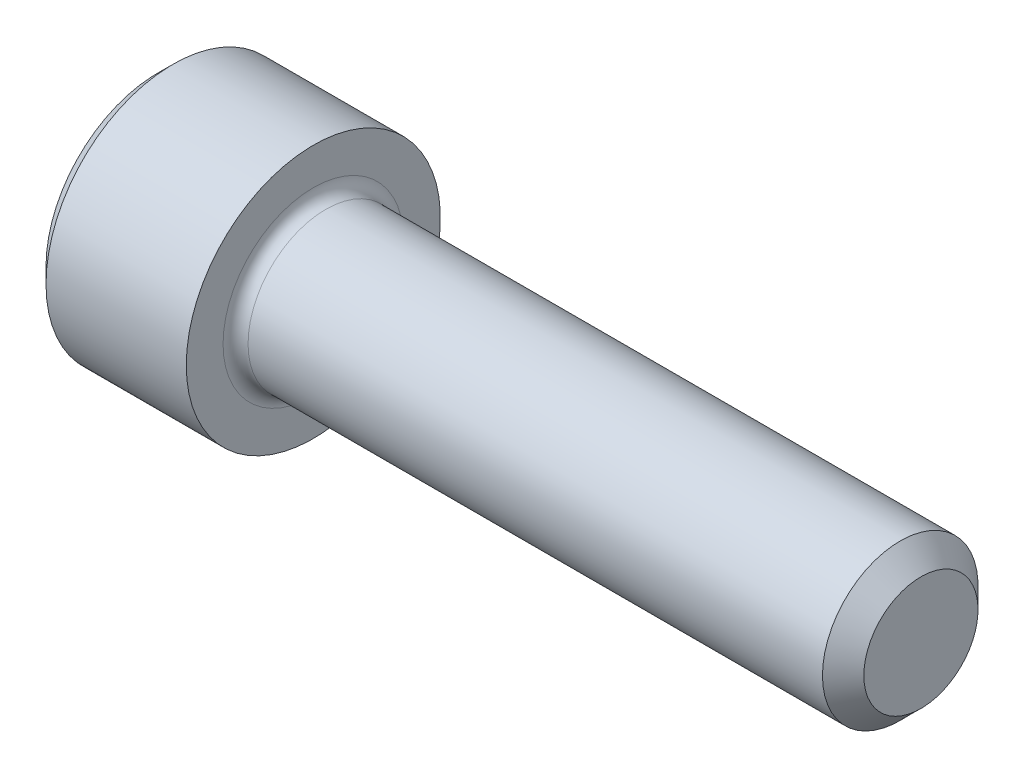
SolidWorks part; units mm, degrees
ref_plane "Plane1" through (0, 0, 0) normal (0, 0, 1) x (1, 0, 0)
ref_plane "Plane2" through (0, 0, 0) normal (0, 1, 0) x (1, 0, 0)
ref_plane "Plane3" through (0, 0, 0) normal (1, 0, 0) x (0, 0, -1)
sketch "BodySke" plane through (0, 0, 0) normal (0, 0, 1) x (1, 0, 0)
  line L0 (0, 0) -> (0, 2.0447)
  line L1 (0.2794, 2.3241) -> (2.8448, 2.3241)
  line L2 (2.8448, 2.3241) -> (2.8448, 1.4224)
  line L3 (2.8448, 1.4224) -> (13.5788, 1.4224)
  line L4 (13.9573, 1.0439) -> (13.9573, 0)
  line L5 (13.9573, 0) -> (0, 0)
  line L6 (-31.75, 0) -> (127, 0) construction
  line L7 (0, 2.0447) -> (0.2794, 2.3241)
  line L8 (13.9573, 1.0439) -> (13.5788, 1.4224)
  line L9 (0, -2.0447) -> (0.2794, -2.3241) construction
  line L10 (13.9573, -1.0439) -> (13.5788, -1.4224) construction
  line L11 (3.4798, 9.525) -> (3.4798, 3.175) construction
  line L12 (2.8448, 9.525) -> (2.8448, 3.175) construction
  line L13 (-24.1427, 9.525) -> (-24.1427, 3.175) construction
  dimension "Diameter" = 2.8448
  dimension "Head_ht" = 2.8448
  dimension "Length" = 11.1125
  dimension "Body_ch_ang" = 45
  dimension "Head_dia" = 4.6482
  dimension "Head_ch_ang" = 45
  dimension "Head_side_ht" = 2.5654
  dimension "Minor_dia" = 2.0879
  dimension "Advance" = 0.635
  dimension "Thread_nom" = 11.1125
  dimension "Thread_length" = 38.1
revolve "Base-Revolve" add sketch "BodySke"
cosmetic thread "ThreadCosmetic"
fillet "Fillet1" radius 0.2286 1 edges at (2.8448, 0, 1.4224)
sketch "Sketch2" plane through (0, 0, 0) normal (0, 0, 1) x (1, 0, 0)
  line L0 (0, 1.1938) -> (1.2954, 1.1938)
  line L1 (1.2954, 1.1938) -> (1.9846, 0)
  line L2 (-31.75, 0) -> (127, 0) construction
  line L3 (1.9846, 0) -> (0, 0)
  line L4 (0, 0) -> (0, 1.1938)
  line L5 (0, 2.0447) -> (0, -2.0447) construction
  line L6 (0, 0) -> (47.625, 0) construction
  line L7 (2.8448, -2.3241) -> (2.8448, 2.3241) construction
  dimension "D1" = 1.1938
  dimension "D2" = 60
  dimension "Wall_thickness" = 1.5494
revolve "Hex-PreBroach" cut sketch "Sketch2" angle 360 about L6
sketch "Sketch3" plane through (0, 0, 0) normal (-1, 0, 0) x (0, 0.5, 0.866)
  line L0 (0.6892, 1.1938) -> (-0.6892, 1.1938)
  line L1 (-0.6892, 1.1938) -> (-1.3785, 0)
  line L2 (0.6892, 1.1938) -> (1.3785, 0)
  line L3 (0.6892, -1.1938) -> (1.3785, 0)
  line L4 (0.6892, -1.1938) -> (-0.6892, -1.1938)
  line L5 (-0.6892, -1.1938) -> (-1.3785, 0)
  dimension "D1" = 1.1938
  dimension "D2" = 1.1938
  dimension "Hex_size" = 2.3876
extrude "Hex" cut sketch "Sketch3" against normal blind 1.2954
sketch "Sketch4" plane through (0, 0, 0) normal (-1, 0, 0) x (0, 0, 1)
  line L0 (0, 0) -> (1.4605, 0)
  line L1 (0, 0) -> (6.1484, 3.5498) construction
  line L2 (0, 0) -> (0.7302, 1.2648)
  line L3 (1.2009, 0.3267) -> (1.3933, 0.4378)
  line L4 (0.8834, 0.8767) -> (1.0758, 0.9877)
  arc A0 (1.2009, 0.3267) -> (0.8834, 0.8767) centre (0, 0) ccw
  arc A1 (1.4605, 0) -> (1.3933, 0.4378) centre (0, 0) ccw
  arc A2 (0.7302, 1.2648) -> (1.0758, 0.9877) centre (0, 0) cw
  dimension "D1" = 30
  dimension "Spline_n_dim" = 2.4892
  dimension "Spline_m_dim" = 2.921
  dimension "D2" = 60
  dimension "D3" = 0.3175
  dimension "Spline_p_dim" = 0.635
extrude "Spline" [suppressed] cut sketch "Sketch4" against normal blind 1.2954
pattern_circular "CirPattern1" [suppressed] count 6 every 60
sketch "Sketch5" plane through (0, 0, 0) normal (0, 0, 1) x (1, 0, 0)
  line L0 (-31.75, 0) -> (127, 0) construction
  line L2 (0, 2.0447) -> (0, -2.0447) construction
  circle A0 centre (1.016, 0) radius 0.4445
  dimension "Drilled_hole_dia" = 0.889
  dimension "Drilled_hole_loc" = 1.016
extrude "Hole" [suppressed] cut sketch "Sketch5" against normal through all and the other way through all
pattern_circular "Drilled-4" [suppressed] count 2 every 60
pattern_circular "Drilled-6" [suppressed] count 3 every 60
sketch "ThdSchSke" plane through (0, 0, 0) normal (0, 0, 1) x (1, 0, 0)
  line L0 (3.4798, -1.0439) -> (3.2148, -1.4224)
  line L1 (3.4798, -1.0439) -> (3.7448, -1.4224)
  line L2 (3.7448, -1.4224) -> (3.7448, -1.778)
  line L3 (-3.175, 0) -> (5.1513, 0) construction
  line L5 (3.7448, -1.778) -> (3.2148, -1.778)
  line L6 (3.2148, -1.778) -> (3.2148, -1.4224)
  line L7 (0, 2.0447) -> (0, -2.0447) construction
  dimension "Thread_minor" = 2.0879
  dimension "Diameter" = 2.8448
  dimension "Start" = 3.4798
  dimension "SideAngle" = 55
  dimension "VeeAngle" = 70
  dimension "Overcut" = 3.556
revolve "ThreadSchematic" [suppressed] cut sketch "ThdSchSke" angle 360 about L3
pattern_linear "ThdSchPat" [suppressed]
equation "\"D2@Sketch3\" = \"Hex_size@Sketch3\" / 2"
equation "\"D1@Sketch3\" = \"Hex_size@Sketch3\" / 2"
equation "\"D1@Sketch2\" = \"Hex_size@Sketch3\" / 2"
equation "\"D3@Sketch4\" = \"Spline_p_dim@Sketch4\" / 2"
equation "\"Thread_minor@ThreadCosmetic\"  =  \"Minor_dia@BodySke\""
equation "\"D2@CirPattern1\" = 360 / \"Num_teeth@CirPattern1\""
equation "\"Wall_thickness@Sketch2\" = \"Head_ht@BodySke\" - \"Key_eng@Hex\""
equation "\"Thread_length@ThreadCosmetic\" = ((sgn( (\"Length@BodySke\" - \"Advance@BodySke\" ) - \"Thread_nom@BodySke\" )-1)*( (\"Length@BodySke\" - \"Advance@BodySke\" ) - \"Thread_nom@BodySke\" ))/-2+ \"Thread_nom@BodySke\""
equation "\"Thread_minor@ThdSchSke\" = \"Minor_dia@BodySke\""
equation "\"Diameter@ThdSchSke\" = \"Diameter@BodySke\""
equation "\"Overcut@ThdSchSke\" = \"Diameter@BodySke\" * 1.25"
equation "\"Start@ThdSchSke\" = \"Head_ht@BodySke\" + \"Length@BodySke\" - \"Thread_length@ThreadCosmetic\"  '---Non-countersunk---"
equation "\"Num_threads@ThdSchPat\" = int( \"Thread_length@ThreadCosmetic\" / \"Advance@BodySke\" + 0.999 )  + 1"
equation "\"Advance@ThdSchPat\" = \"Thread_length@ThreadCosmetic\" /  (\"Num_threads@ThdSchPat\" - 1) 'relax it"
equation "\"Num_threads@ThdSchPat\" = \"Num_threads@ThdSchPat\" - sgn( \"Num_threads@ThdSchPat\" - 1) '---chamfered tips only---"
